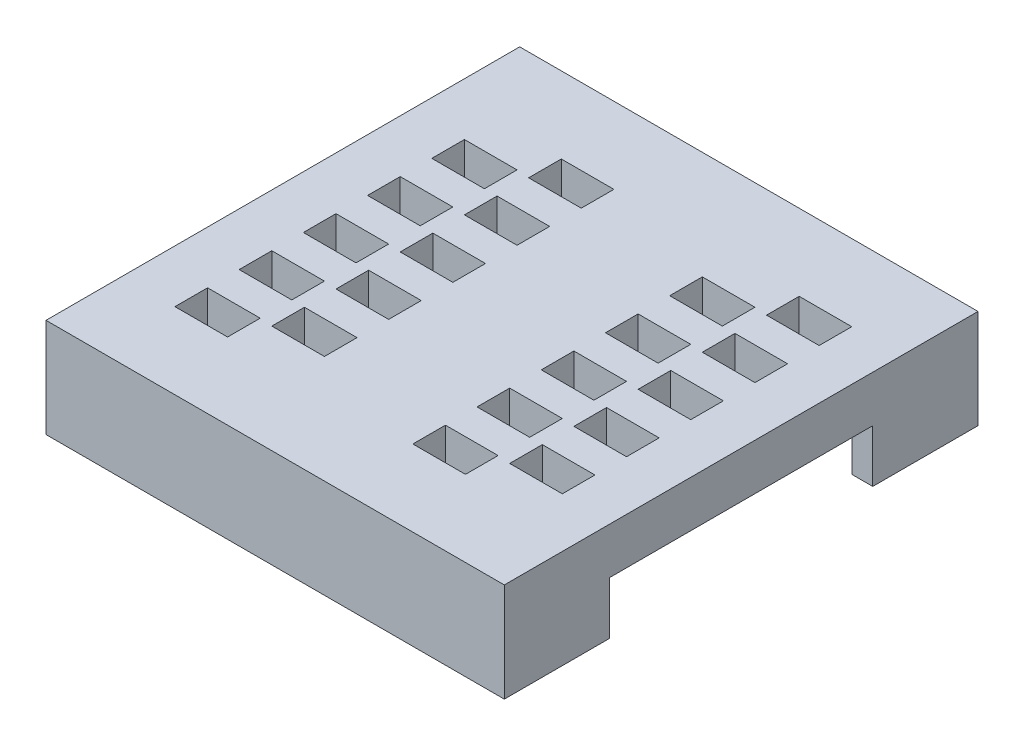
SolidWorks part; units mm, degrees
ref_plane "Спереди" through (0, 0, 0) normal (0, 0, 1) x (1, 0, 0)
ref_plane "Сверху" through (0, 0, 0) normal (0, 1, 0) x (1, 0, 0)
ref_plane "Справа" through (0, 0, 0) normal (1, 0, 0) x (0, 0, -1)
sketch "Эскиз1" plane through (0, 0, 0) normal (0, 1, 0) x (1, 0, 0)
  line L0 (-148.5, -105) -> (-104.9604, -105)
  line L1 (-104.9604, -105) -> (-104.9604, -60)
  line L2 (-104.9604, -60) -> (-148.5, -60)
  line L3 (-148.5, -60) -> (-148.5, -105)
  line L4 (-143.5, -97.7503) -> (-138.5, -97.7503)
  line L5 (-138.5, -97.7503) -> (-138.5, -94.6503)
  line L6 (-138.5, -94.6503) -> (-143.5, -94.6503)
  line L7 (-143.5, -94.6503) -> (-143.5, -97.7503)
  line L8 (-120.9, -97.7503) -> (-115.9, -97.7503)
  line L9 (-115.9, -97.7503) -> (-115.9, -94.6503)
  line L10 (-115.9, -94.6503) -> (-120.9, -94.6503)
  line L11 (-120.9, -94.6503) -> (-120.9, -97.7503)
  line L12 (-114.7, -94.7503) -> (-109.7, -94.7503)
  line L13 (-109.7, -94.7503) -> (-109.7, -91.6503)
  line L14 (-109.7, -91.6503) -> (-114.7, -91.6503)
  line L15 (-114.7, -91.6503) -> (-114.7, -94.7503)
  line L16 (-137.3, -94.7503) -> (-132.3, -94.7503)
  line L17 (-132.3, -94.7503) -> (-132.3, -91.6503)
  line L18 (-132.3, -91.6503) -> (-137.3, -91.6503)
  line L19 (-137.3, -91.6503) -> (-137.3, -94.7503)
  line L20 (-114.7, -88.6503) -> (-109.7, -88.6503)
  line L21 (-109.7, -88.6503) -> (-109.7, -85.5503)
  line L22 (-109.7, -85.5503) -> (-114.7, -85.5503)
  line L23 (-114.7, -85.5503) -> (-114.7, -88.6503)
  line L24 (-137.3, -88.6503) -> (-132.3, -88.6503)
  line L25 (-132.3, -88.6503) -> (-132.3, -85.5503)
  line L26 (-132.3, -85.5503) -> (-137.3, -85.5503)
  line L27 (-137.3, -85.5503) -> (-137.3, -88.6503)
  line L28 (-143.5, -91.6503) -> (-138.5, -91.6503)
  line L29 (-138.5, -91.6503) -> (-138.5, -88.5503)
  line L30 (-138.5, -88.5503) -> (-143.5, -88.5503)
  line L31 (-143.5, -88.5503) -> (-143.5, -91.6503)
  line L32 (-120.9, -91.6503) -> (-115.9, -91.6503)
  line L33 (-115.9, -91.6503) -> (-115.9, -88.5503)
  line L34 (-115.9, -88.5503) -> (-120.9, -88.5503)
  line L35 (-120.9, -88.5503) -> (-120.9, -91.6503)
  line L36 (-114.7, -76.4503) -> (-109.7, -76.4503)
  line L37 (-109.7, -76.4503) -> (-109.7, -73.3503)
  line L38 (-109.7, -73.3503) -> (-114.7, -73.3503)
  line L39 (-114.7, -73.3503) -> (-114.7, -76.4503)
  line L40 (-137.3, -76.4503) -> (-132.3, -76.4503)
  line L41 (-132.3, -76.4503) -> (-132.3, -73.3503)
  line L42 (-132.3, -73.3503) -> (-137.3, -73.3503)
  line L43 (-137.3, -73.3503) -> (-137.3, -76.4503)
  line L44 (-143.5, -79.4503) -> (-138.5, -79.4503)
  line L45 (-138.5, -79.4503) -> (-138.5, -76.3503)
  line L46 (-138.5, -76.3503) -> (-143.5, -76.3503)
  line L47 (-143.5, -76.3503) -> (-143.5, -79.4503)
  line L48 (-120.9, -79.4503) -> (-115.9, -79.4503)
  line L49 (-115.9, -79.4503) -> (-115.9, -76.3503)
  line L50 (-115.9, -76.3503) -> (-120.9, -76.3503)
  line L51 (-120.9, -76.3503) -> (-120.9, -79.4503)
  line L52 (-143.5, -85.5503) -> (-138.5, -85.5503)
  line L53 (-138.5, -85.5503) -> (-138.5, -82.4503)
  line L54 (-138.5, -82.4503) -> (-143.5, -82.4503)
  line L55 (-143.5, -82.4503) -> (-143.5, -85.5503)
  line L56 (-120.9, -85.5503) -> (-115.9, -85.5503)
  line L57 (-115.9, -85.5503) -> (-115.9, -82.4503)
  line L58 (-115.9, -82.4503) -> (-120.9, -82.4503)
  line L59 (-120.9, -82.4503) -> (-120.9, -85.5503)
  line L60 (-114.7, -82.5503) -> (-109.7, -82.5503)
  line L61 (-109.7, -82.5503) -> (-109.7, -79.4503)
  line L62 (-109.7, -79.4503) -> (-114.7, -79.4503)
  line L63 (-114.7, -79.4503) -> (-114.7, -82.5503)
  line L64 (-137.3, -82.5503) -> (-132.3, -82.5503)
  line L65 (-132.3, -82.5503) -> (-132.3, -79.4503)
  line L66 (-132.3, -79.4503) -> (-137.3, -79.4503)
  line L67 (-137.3, -79.4503) -> (-137.3, -82.5503)
  line L68 (-143.5, -73.3503) -> (-138.5, -73.3503)
  line L69 (-138.5, -73.3503) -> (-138.5, -70.2503)
  line L70 (-138.5, -70.2503) -> (-143.5, -70.2503)
  line L71 (-143.5, -70.2503) -> (-143.5, -73.3503)
  line L72 (-120.9, -73.3503) -> (-115.9, -73.3503)
  line L73 (-115.9, -73.3503) -> (-115.9, -70.2503)
  line L74 (-115.9, -70.2503) -> (-120.9, -70.2503)
  line L75 (-120.9, -70.2503) -> (-120.9, -73.3503)
  line L76 (-114.7, -70.3503) -> (-109.7, -70.3503)
  line L77 (-109.7, -70.3503) -> (-109.7, -67.2503)
  line L78 (-109.7, -67.2503) -> (-114.7, -67.2503)
  line L79 (-114.7, -67.2503) -> (-114.7, -70.3503)
  line L80 (-137.3, -70.3503) -> (-132.3, -70.3503)
  line L81 (-132.3, -70.3503) -> (-132.3, -67.2503)
  line L82 (-132.3, -67.2503) -> (-137.3, -67.2503)
  line L83 (-137.3, -67.2503) -> (-137.3, -70.3503)
sketch "Эскиз2" plane through (0, 0, 0) normal (0, 1, 0) x (1, 0, 0)
  line L0 (-148.5, -105) -> (-104.8684, -105)
  line L1 (-104.8684, -105) -> (-104.8684, -60)
  line L2 (-104.8684, -60) -> (-148.5, -60)
  line L3 (-148.5, -60) -> (-148.5, -105)
  line L4 (-137.4, -71.4) -> (-132.2, -71.4)
  line L5 (-132.2, -71.4) -> (-132.2, -66.2)
  line L6 (-132.2, -66.2) -> (-137.4, -66.2)
  line L7 (-137.4, -66.2) -> (-137.4, -71.4)
  line L8 (-137.4, -77.5) -> (-132.2, -77.5)
  line L9 (-132.2, -77.5) -> (-132.2, -72.3)
  line L10 (-132.2, -72.3) -> (-137.4, -72.3)
  line L11 (-137.4, -72.3) -> (-137.4, -77.5)
  line L12 (-137.4, -83.6) -> (-132.2, -83.6)
  line L13 (-132.2, -83.6) -> (-132.2, -78.4)
  line L14 (-132.2, -78.4) -> (-137.4, -78.4)
  line L15 (-137.4, -78.4) -> (-137.4, -83.6)
  line L16 (-137.4, -89.7) -> (-132.2, -89.7)
  line L17 (-132.2, -89.7) -> (-132.2, -84.5)
  line L18 (-132.2, -84.5) -> (-137.4, -84.5)
  line L19 (-137.4, -84.5) -> (-137.4, -89.7)
  line L20 (-137.4, -95.8003) -> (-132.2, -95.8003)
  line L21 (-132.2, -95.8003) -> (-132.2, -90.6003)
  line L22 (-132.2, -90.6003) -> (-137.4, -90.6003)
  line L23 (-137.4, -90.6003) -> (-137.4, -95.8003)
  line L24 (-121, -74.4003) -> (-115.8, -74.4003)
  line L25 (-115.8, -74.4003) -> (-115.8, -69.2003)
  line L26 (-115.8, -69.2003) -> (-121, -69.2003)
  line L27 (-121, -69.2003) -> (-121, -74.4003)
  line L28 (-121, -80.5003) -> (-115.8, -80.5003)
  line L29 (-115.8, -80.5003) -> (-115.8, -75.3003)
  line L30 (-115.8, -75.3003) -> (-121, -75.3003)
  line L31 (-121, -75.3003) -> (-121, -80.5003)
  line L32 (-121, -86.6003) -> (-115.8, -86.6003)
  line L33 (-115.8, -86.6003) -> (-115.8, -81.4003)
  line L34 (-115.8, -81.4003) -> (-121, -81.4003)
  line L35 (-121, -81.4003) -> (-121, -86.6003)
  line L36 (-121, -92.7003) -> (-115.8, -92.7003)
  line L37 (-115.8, -92.7003) -> (-115.8, -87.5003)
  line L38 (-115.8, -87.5003) -> (-121, -87.5003)
  line L39 (-121, -87.5003) -> (-121, -92.7003)
  line L40 (-121, -98.8003) -> (-115.8, -98.8003)
  line L41 (-115.8, -98.8003) -> (-115.8, -93.6003)
  line L42 (-115.8, -93.6003) -> (-121, -93.6003)
  line L43 (-121, -93.6003) -> (-121, -98.8003)
  ellipse E0 centre (-143.5, -65) end of major axis (-143.5, -64) minor radius 1
  ellipse E1 centre (-143.5, -100) end of major axis (-143.5, -99) minor radius 1
  ellipse E2 centre (-109.7, -65) end of major axis (-109.7, -64) minor radius 1
  ellipse E3 centre (-109.7, -100) end of major axis (-109.7, -99) minor radius 1
extrude "Бобышка-Вытянуть1" add sketch "Эскиз1" along normal blind 3.4
extrude "Бобышка-Вытянуть2" add sketch "Эскиз2" against normal blind 1
sketch "Эскиз6" plane through (0, 0, 60) normal (0, 0, -1) x (-1, 0, 0)
  line L0 (104.8684, 0) -> (104.9604, 0) construction
  line L1 (104.8684, -1) -> (104.9604, -1)
  line L2 (104.8684, -1) -> (104.8684, 0)
  line L3 (104.8684, 0) -> (104.9604, 0)
  line L4 (104.9604, -1) -> (104.9604, 0)
extrude "Вырез-Вытянуть2" cut sketch "Эскиз6" against normal through all
sketch "Эскиз3" plane through (0, -1, 0) normal (0, -1, 0) x (1, 0, 0)
  circle A0 centre (-143.5, 100) radius 1
  circle A1 centre (-143.5, 100) radius 4
  circle A2 centre (-109.7, 100) radius 1
  circle A3 centre (-109.7, 100) radius 4
  circle A4 centre (-143.5, 65) radius 1
  circle A5 centre (-143.5, 65) radius 4
  circle A6 centre (-109.7, 65) radius 1
  circle A7 centre (-109.7, 65) radius 4
  dimension "D1" = 2
  dimension "D2" = 8
extrude "Бобышка-Вытянуть3" add sketch "Эскиз3" along normal blind 1.2
sketch "Эскиз4" plane through (0, -1, 0) normal (0, -1, 0) x (1, 0, 0)
  line L0 (-104.9604, 60) -> (-148.5, 60) construction
  line L1 (-148.5, 105) -> (-104.9604, 105)
  line L2 (-148.5, 105) -> (-148.5, 60)
  line L3 (-148.5, 60) -> (-104.9604, 60)
  line L4 (-104.9604, 105) -> (-104.9604, 60)
  line L5 (-104.9604, 105) -> (-104.9604, 60) construction
  line L7 (-146.51, 103.01) -> (-106.9504, 103.01)
  line L8 (-146.51, 103.01) -> (-146.51, 61.99)
  line L9 (-146.51, 61.99) -> (-106.9504, 61.99)
  line L10 (-106.9504, 103.01) -> (-106.9504, 61.99)
  dimension "D1" = 1.99
  dimension "D2" = 1.99
  dimension "D3" = 1.99
  dimension "D4" = 1.99
extrude "Бобышка-Вытянуть4" add sketch "Эскиз4" along normal blind 5
sketch "Эскиз5" plane through (0, -6, 0) normal (0, -1, 0) x (1, 0, 0)
  line L1 (-148.5, 105) -> (-148.5, 60) construction
  line L2 (-148.5, 95) -> (-146.51, 95)
  line L3 (-148.5, 95) -> (-148.5, 70)
  line L4 (-148.5, 70) -> (-146.51, 70)
  line L7 (-146.51, 95) -> (-146.51, 70)
  line L8 (-146.51, 103.01) -> (-146.51, 61.99) construction
  line L9 (-106.9504, 61.99) -> (-106.9504, 103.01) construction
  line L10 (-106.9504, 95) -> (-104.9604, 95)
  line L14 (-106.9504, 95) -> (-106.9504, 70)
  line L15 (-106.9504, 70) -> (-104.9604, 70)
  line L16 (-104.9604, 95) -> (-104.9604, 70)
  line L17 (-104.9604, 60) -> (-104.9604, 105) construction
  line L18 (-104.9604, 105) -> (-148.5, 105) construction
  line L19 (-148.5, 60) -> (-104.9604, 60) construction
  dimension "D1" = 10
  dimension "D2" = 10
  dimension "D3" = 10
  dimension "D4" = 10
extrude "Вырез-Вытянуть1" cut sketch "Эскиз5" against normal blind 5
